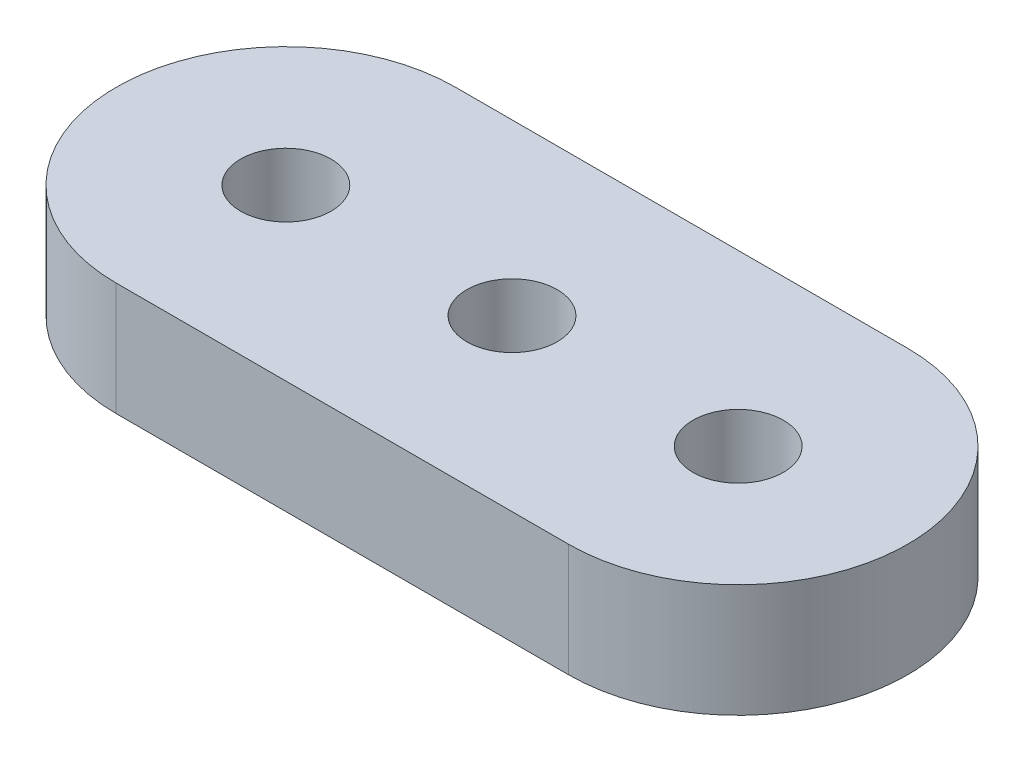
SolidWorks part; units mm, degrees
ref_plane "Front Plane" through (0, 0, 0) normal (0, 0, 1) x (1, 0, 0)
ref_plane "Top Plane" through (0, 0, 0) normal (0, 1, 0) x (1, 0, 0)
ref_plane "Right Plane" through (0, 0, 0) normal (1, 0, 0) x (0, 0, -1)
sketch "Sketch1" plane through (0, 0, 0) normal (0, 1, 0) x (1, 0, 0)
  line L0 (0, 0) -> (10.16, 0)
  line L1 (0, 7.62) -> (10.16, 7.62)
  arc A0 (0, 0) -> (0, 7.62) centre (0, 3.81) cw
  arc A1 (10.16, 7.62) -> (10.16, 0) centre (10.16, 3.81) cw
  dimension "D2" = 3.81
  dimension "D1" = 10.16
extrude "Boss-Extrude1" add sketch "Sketch1" along normal blind 2.54
sketch "Sketch2" plane through (0, 2.54, 0) normal (0, 1, 0) x (1, 0, 0)
  line L0 (-3.81, 3.81) -> (13.97, 3.81) construction
  arc A0 (0, 7.62) -> (0, 0) centre (0, 3.81) ccw construction
  arc A1 (10.16, 0) -> (10.16, 7.62) centre (10.16, 3.81) ccw construction
  circle A2 centre (0, 3.81) radius 1.016
  circle A3 centre (5.08, 3.81) radius 1.016
  circle A4 centre (10.16, 3.81) radius 1.016
  dimension "D1" = 2.032
  dimension "D2" = 5.08
  dimension "D3" = 5.08
extrude "Cut-Extrude1" cut sketch "Sketch2" against normal through all
